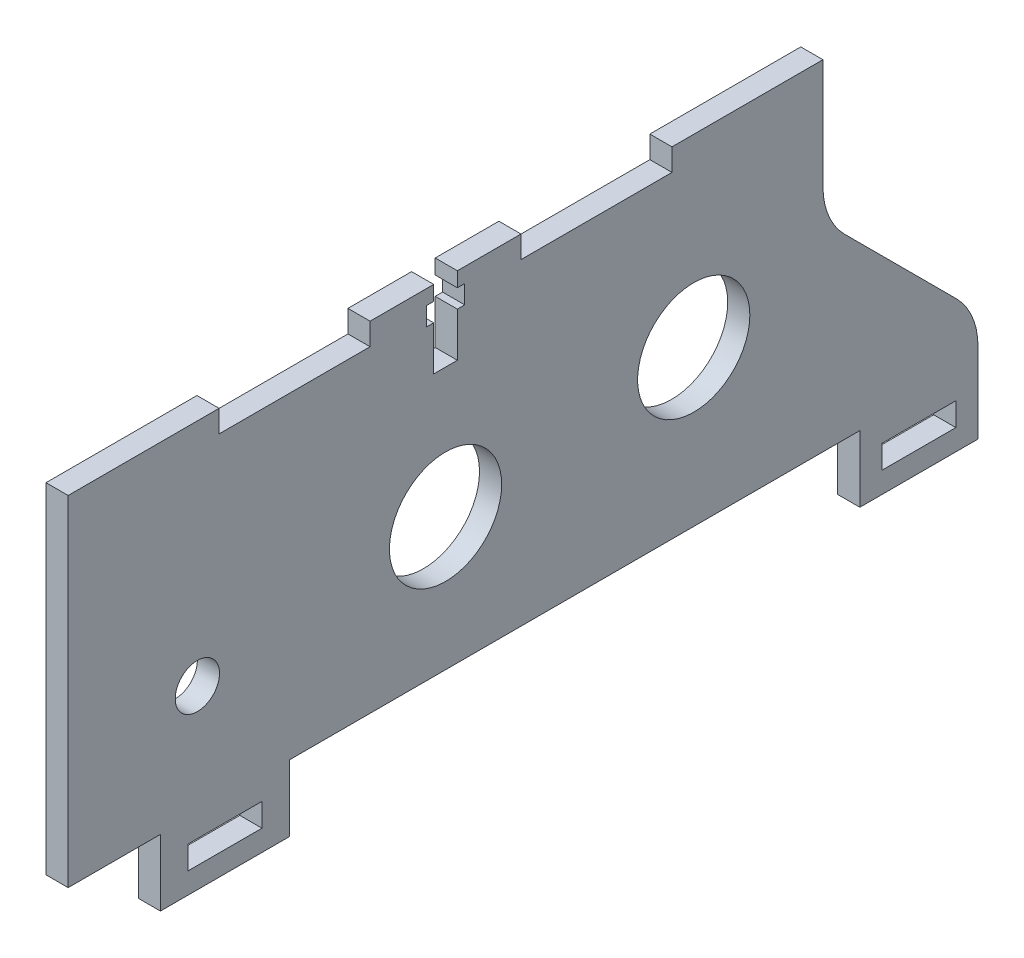
SolidWorks part; units mm, degrees
ref_plane "Front Plane" through (0, 0, 0) normal (0, 0, 1) x (1, 0, 0)
ref_plane "Top Plane" through (0, 0, 0) normal (0, 1, 0) x (1, 0, 0)
ref_plane "Right Plane" through (0, 0, 0) normal (1, 0, 0) x (0, 0, -1)
sketch "Sketch1" plane through (0, 0, 0) normal (1, 0, 0) x (0, 0, -1)
  line L0 (0, 0) -> (0, 46)
  line L3 (123.2238, -9) -> (107.2238, -9)
  line L4 (107.2238, -9) -> (107.2238, 0)
  line L9 (107.2238, 0) -> (30, 0)
  line L12 (0, 0) -> (12.5, 0)
  line L17 (12.5, 0) -> (12.5, -9)
  line L18 (12.5, -9) -> (30, -9)
  line L19 (30, -9) -> (30, 0)
  line L20 (0, 46) -> (20.4448, 46)
  line L21 (20.4448, 46) -> (20.4448, 43)
  line L22 (20.4448, 43) -> (40.8895, 43)
  line L23 (40.8895, 43) -> (40.8895, 46)
  line L24 (40.8895, 46) -> (61.3343, 46)
  line L25 (61.3343, 46) -> (61.3343, 43)
  line L26 (61.3343, 43) -> (81.779, 43)
  line L27 (81.779, 43) -> (81.779, 46)
  line L28 (81.779, 46) -> (102.2238, 46)
  line L29 (17.5, 14.9) -> (84.7238, 21) construction
  line L30 (102.2238, 46) -> (102.2238, 6)
  line L32 (123.2238, 6) -> (123.2238, -9)
  line L37 (102.2238, 6) -> (123.2238, 6)
  line L40 (102.2238, 27) -> (123.2238, 6)
  line L41 (16.25, -6.15) -> (26.25, -6.15)
  line L42 (16.25, -6.15) -> (16.25, -3)
  line L43 (16.25, -3) -> (26.25, -3)
  line L44 (26.25, -6.15) -> (26.25, -3)
  line L45 (16.25, -6.15) -> (26.25, -3) construction
  line L46 (16.25, -3) -> (26.25, -6.15) construction
  line L47 (110.2238, -6.15) -> (120.2238, -6.15)
  line L48 (110.2238, -6.15) -> (110.2238, -3)
  line L49 (110.2238, -3) -> (120.2238, -3)
  line L50 (120.2238, -6.15) -> (120.2238, -3)
  line L51 (110.2238, -6.15) -> (120.2238, -3) construction
  line L52 (110.2238, -3) -> (120.2238, -6.15) construction
  circle A0 centre (17.5, 14.9) radius 3
  circle A1 centre (51.1119, 17.95) radius 7.6
  circle A2 centre (84.7238, 21) radius 7.6
  point P9 (115.2238, -4.575)
  point P14 (21.25, -4.575)
  point P20 (21.25, -9)
  point P21 (115.2238, -9)
  point P37 (51.1119, 17.95)
  point P41 (17.5, 14.9)
  point P42 (51.1119, 17.95)
  point P43 (84.7238, 21)
  dimension "D10" = 6
  dimension "D11" = 15.2
  dimension "D2" = 46
  dimension "D3" = 9
  dimension "D4" = 14.9
  dimension "D5" = 67.5
  dimension "D6" = 17.5
  dimension "D7" = 17.5
  dimension "D8" = 21
  dimension "D9" = 3
  dimension "D12" = 5
  dimension "D13" = 16
  dimension "D14" = 15
  dimension "D15" = 17.5
  dimension "D16" = 3
  dimension "D17" = 10
  dimension "D18" = 3.15
  dimension "D19" = 12.5
  dimension "D20" = 45
extrude "Boss-Extrude1" add sketch "Sketch1" along normal blind 3 contours L40 L30 L37 | L37 L30 L28 L27 L26 L25 L24 L23 L22 L21 L20 L0 L12 L17 L18 L19 L9 L4 L3 L32 A2 A1 A0 L50 L47 L48 L49 L44 L41 L42 L43
fillet "Fillet1" radius 10 2 edges at (1.5, 6, -123.2238) (1.5, 27, -102.2238)
sketch "Sketch2" plane through (3, 0, 0) normal (1, 0, 0) x (0, 0, -1)
  line L0 (40.8895, 46) -> (61.3343, 46) construction
  line L1 (48.5119, 41.5) -> (53.7119, 41.5)
  line L2 (48.5119, 41.5) -> (48.5119, 44)
  line L3 (48.5119, 44) -> (53.7119, 44)
  line L4 (53.7119, 41.5) -> (53.7119, 44)
  line L5 (48.5119, 41.5) -> (53.7119, 44) construction
  line L6 (48.5119, 44) -> (53.7119, 41.5) construction
  line L7 (49.5119, 46) -> (52.7119, 46)
  line L8 (49.5119, 46) -> (49.5119, 35.5)
  line L9 (49.5119, 35.5) -> (52.7119, 35.5)
  line L10 (52.7119, 46) -> (52.7119, 35.5)
  line L11 (49.5119, 46) -> (52.7119, 35.5) construction
  line L12 (49.5119, 35.5) -> (52.7119, 46) construction
  point P0 (51.1119, 42.75)
  point P5 (51.1119, 40.75)
  point P13 (51.1119, 46)
  line M15 (61.3343, 46) -> (40.8895, 46)
  dimension "D1" = 10.5
  dimension "D2" = 3.2
  dimension "D3" = 5.2
  dimension "D4" = 2
  dimension "D5" = 2.5
extrude "Cut-Extrude1" cut sketch "Sketch2" against normal through all both and the other way through all contours L10 L1 L8 L9 | L10 L3 L8 L1 | L8 L3 L2 L1 | L10 L8 L3 M15 | L3 L10 L1 L4
